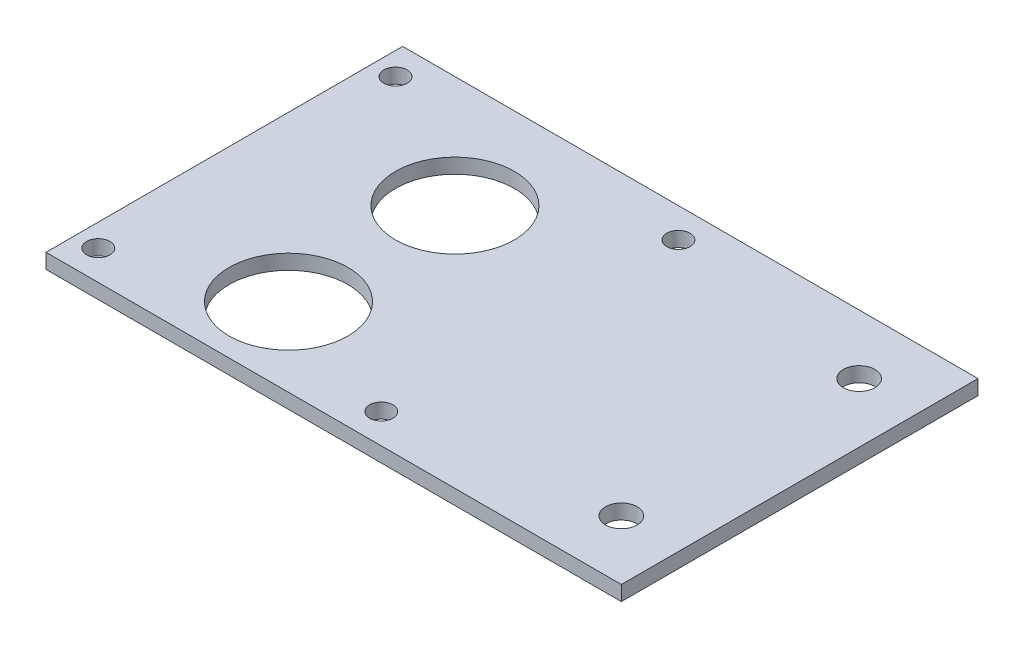
SolidWorks part; units mm, degrees
ref_plane "Front Plane" through (0, 0, 0) normal (0, 0, 1) x (1, 0, 0)
ref_plane "Top Plane" through (0, 0, 0) normal (0, 1, 0) x (1, 0, 0)
ref_plane "Right Plane" through (0, 0, 0) normal (1, 0, 0) x (0, 0, -1)
sketch "Sketch2" plane through (0, 0, 0) normal (0, 1, 0) x (1, 0, 0)
  line L0 (0, 76.2) -> (0, 0)
  line L1 (0, 0) -> (122.936, 0)
  line L2 (122.936, 0) -> (122.936, 76.2)
  line L3 (122.936, 76.2) -> (0, 76.2)
  line L4 (-2.6194, 0) -> (2.6194, 0) construction
  line L5 (0, -2.6194) -> (0, 2.6194) construction
  dimension "D1" = 76.2
  dimension "D2" = 122.936
extrude "Boss-Extrude1" add sketch "Sketch2" along normal blind 3.175 contours L0 L1 L2 L3
hole_wizard "#10 (0.1935) Diameter Hole1" positions "Sketch3" profile "Sketch4" hole size "#10" standard "ANSI Inch" end condition through all
sketch "Sketch3" plane through (0, 3.175, 0) normal (0, 1, 0) x (1, 0, 0)
  line L0 (122.936, 76.2) -> (0, 76.2) construction
  line L1 (0, 76.2) -> (0, 0) construction
  point P0 (4.826, 69.85)
  dimension "D1" = 6.35
  dimension "D2" = 4.826
sketch "Sketch4" plane through (4.826, 3.175, -69.85) normal (1, 0, 0) x (0, 0, 1)
  line L0 (0, 0) -> (0, 3.175)
  line L1 (0, 3.175) -> (2.4892, 3.175)
  line L2 (2.4892, 3.175) -> (2.4892, 0)
  line L5 (2.4892, 0) -> (0, 0)
  line L11 (0, -6.35) -> (0, 107.95) construction
  dimension "Thru Hole Dia." = 4.9784
  dimension "Thru Hole Depth" = 3.175
pattern_linear "LPattern1" count 2 spacing 60.452 along (1, 0, 0) of "#10 (0.1935) Diameter Hole1"
hole_wizard "1/4 (0.25) Diameter Hole1" positions "Sketch5" profile "Sketch6" hole size "1/4" standard "ANSI Inch" end condition through all
sketch "Sketch5" plane through (0, 3.175, 0) normal (0, 1, 0) x (1, 0, 0)
  line L0 (122.936, 0) -> (122.936, 76.2) construction
  line L1 (122.936, 76.2) -> (0, 76.2) construction
  point P0 (110.236, 63.5)
  dimension "D1" = 12.7
  dimension "D2" = 12.7
sketch "Sketch6" plane through (110.236, 3.175, -63.5) normal (1, 0, 0) x (0, 0, 1)
  line L0 (0, 0) -> (0, 3.175)
  line L1 (0, 3.175) -> (3.3782, 3.175)
  line L2 (3.3782, 3.175) -> (3.3782, 0)
  line L5 (3.3782, 0) -> (0, 0)
  line L11 (0, -6.35) -> (0, 107.95) construction
  dimension "Thru Hole Dia." = 6.7564
  dimension "Thru Hole Depth" = 3.175
ref_plane "Plane1" through (0, 0, -38.1) normal (0, 0, -1) x (-1, 0, 0)
mirror "Mirror1" about plane through (0, 0, -38.1) normal (0, 0, -1) of "1/4 (0.25) Diameter Hole1", "LPattern1", "#10 (0.1935) Diameter Hole1"
sketch "Sketch7" plane through (0, 3.175, 0) normal (0, 1, 0) x (1, 0, 0)
  line L0 (0, 0) -> (122.936, 0) construction
  line L2 (35.052, 16.764) -> (35.052, 52.324) construction
  line L3 (122.936, 76.2) -> (0, 76.2) construction
  circle A1 centre (35.052, 16.764) radius 12.7
  circle A2 centre (35.052, 52.324) radius 12.7
  circle A3 centre (4.826, 6.35) radius 2.4892 construction
  dimension "D1" = 25.4
  dimension "D4" = 25.4
  dimension "D5" = 23.876
  dimension "D3" = 30.226
  dimension "D2" = 16.764
extrude "Cut-Extrude1" cut sketch "Sketch7" against normal through all
